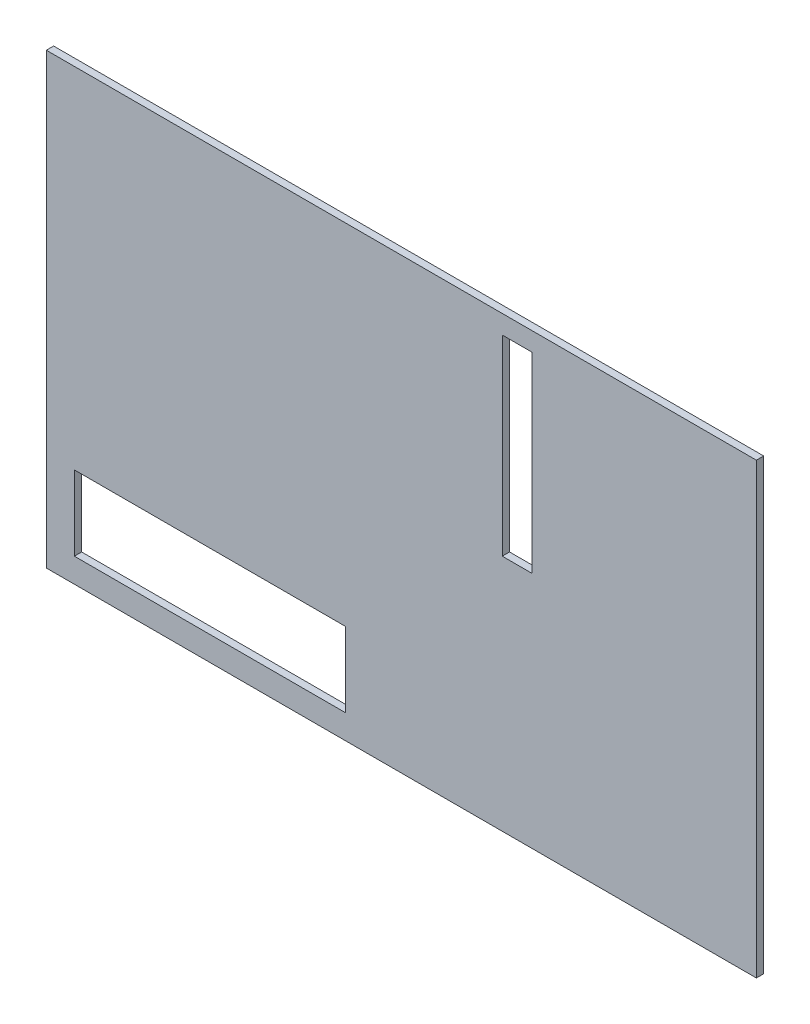
SolidWorks part; units mm, degrees
ref_plane "Front Plane" through (0, 0, 0) normal (0, 0, 1) x (1, 0, 0)
ref_plane "Top Plane" through (0, 0, 0) normal (0, 1, 0) x (1, 0, 0)
ref_plane "Right Plane" through (0, 0, 0) normal (1, 0, 0) x (0, 0, -1)
sketch "Sketch1" plane through (0, 0, 0) normal (0, 0, 1) x (1, 0, 0)
  line L1 (-48.26, -30.48) -> (48.26, -30.48)
  line L2 (-48.26, -30.48) -> (-48.26, 30.48)
  line L3 (-48.26, 30.48) -> (48.26, 30.48)
  line L4 (48.26, -30.48) -> (48.26, 30.48)
  line L5 (-48.26, -30.48) -> (48.26, 30.48) construction
  line L6 (-48.26, 30.48) -> (48.26, -30.48) construction
  point P0 (0, 0)
  dimension "D1" = 96.52
  dimension "D2" = 60.96
extrude "Boss-Extrude1" add sketch "Sketch1" along normal blind 0.9906
sketch "Sketch2" plane through (0, 0, 0.9906) normal (0, 0, 1) x (1, 0, 0)
  line L0 (-48.26, -30.48) -> (48.26, -30.48) construction
  line L1 (-44.45, -17.018) -> (-7.62, -17.018)
  line L2 (-44.45, -17.018) -> (-44.45, -27.178)
  line L3 (-44.45, -27.178) -> (-7.62, -27.178)
  line L4 (-7.62, -17.018) -> (-7.62, -27.178)
  line L5 (-48.26, 30.48) -> (-48.26, -30.48) construction
  line L6 (48.26, 30.48) -> (-48.26, 30.48) construction
  line L7 (13.716, 27.94) -> (17.78, 27.94)
  line L8 (13.716, 27.94) -> (13.716, 1.905)
  line L9 (13.716, 1.905) -> (17.78, 1.905)
  line L10 (17.78, 27.94) -> (17.78, 1.905)
  line L11 (48.26, -30.48) -> (48.26, 30.48) construction
  dimension "D1" = 36.83
  dimension "D2" = 3.302
  dimension "D3" = 3.81
  dimension "D4" = 10.16
  dimension "D5" = 26.035
  dimension "D6" = 4.064
  dimension "D7" = 2.54
  dimension "D8" = 30.48
extrude "Cut-Extrude1" cut sketch "Sketch2" against normal up to next
